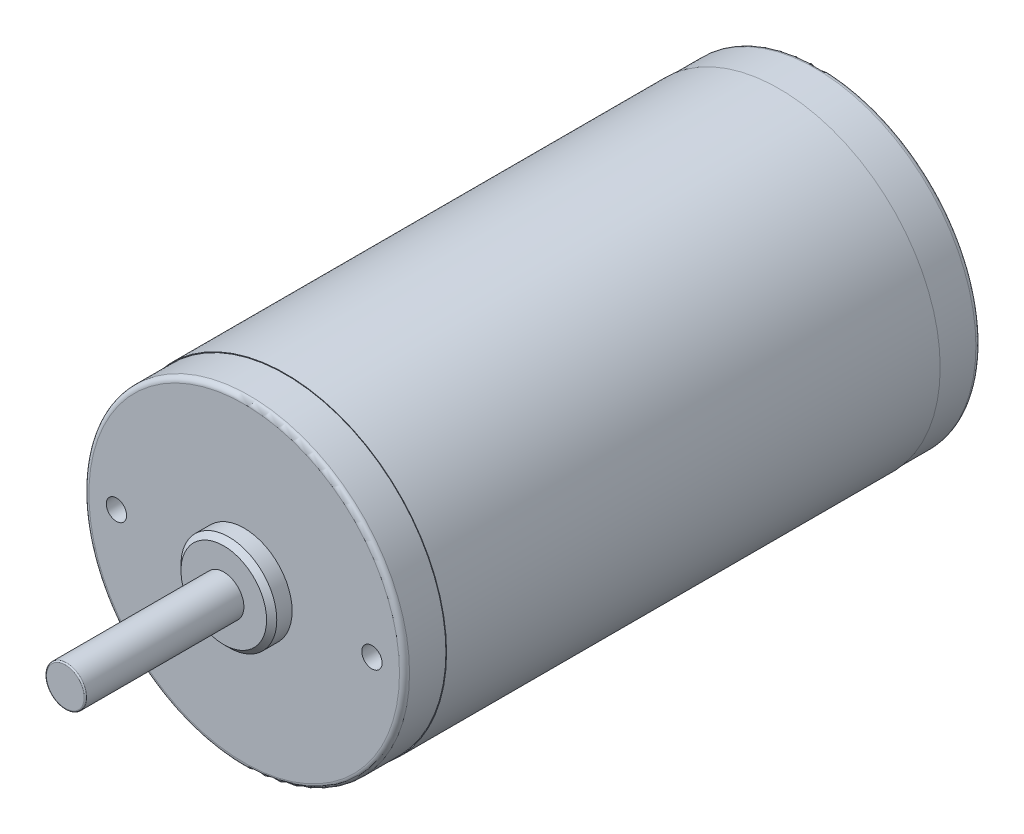
SolidWorks part; units mm, degrees
ref_plane "Front Plane" through (0, 0, 0) normal (0, 0, 1) x (1, 0, 0)
ref_plane "Top Plane" through (0, 0, 0) normal (0, 1, 0) x (1, 0, 0)
ref_plane "Right Plane" through (0, 0, 0) normal (1, 0, 0) x (0, 0, -1)
ref_plane "Plane1" through (0, 109.2962, 0) normal (0, -1, 0) x (1, 0, 0)
sketch "Sketch1" plane through (0, 109.2962, 0) normal (0, -1, 0) x (1, 0, 0)
  line L0 (67.564, 10.8204) -> (35.56, 10.8204)
  line L1 (35.56, 10.8204) -> (35.56, -87.3252)
  line L2 (35.56, -87.3252) -> (67.564, -87.3252)
  line L3 (67.564, -87.3252) -> (67.564, 10.8204)
  line L4 (35.56, 10.8204) -> (35.56, -87.3252) construction
revolve "Revolve1" add sketch "Sketch1" angle 360 about L4
sketch "Sketch2" plane through (0, 0, 10.8204) normal (0, 0, 1) x (1, 0, 0)
  circle A0 centre (35.56, 109.2962) radius 31.877
extrude "Boss-Extrude1" add sketch "Sketch2" along normal blind 8.2296
ref_plane "Plane2" through (0, 0, 18.542) normal (0, 0, -1) x (-1, 0, 0)
sketch "Sketch5" plane through (0, 0, 18.542) normal (0, 0, -1) x (-1, 0, 0)
  circle A0 centre (-35.56, 109.2962) radius 9.525
extrude "Boss-Extrude2" add sketch "Sketch5" against normal blind 4.572
sketch "Sketch6" plane through (0, 0, 23.114) normal (0, 0, 1) x (1, 0, 0)
  circle A0 centre (35.56, 109.2962) radius 4
extrude "Boss-Extrude3" add sketch "Sketch6" along normal blind 31.5
sketch "Sketch8" plane through (0, 0, -87.3252) normal (0, 0, -1) x (-1, 0, 0)
  circle A0 centre (-35.56, 109.2962) radius 31.877
extrude "Boss-Extrude4" add sketch "Sketch8" along normal blind 8.2296
sketch "Sketch9" plane through (0, 0, -95.5548) normal (0, 0, -1) x (-1, 0, 0)
  circle A0 centre (-35.56, 109.2962) radius 15.0368
extrude "Boss-Extrude5" add sketch "Sketch9" along normal blind 4.7625
ref_plane "Plane3" [suppressed] through (0, 120.5036, 0) normal (0, 1, 0) x (-1, 0, 0)
ref_plane "Plane4" [suppressed] through (0, 127.9033, 0) normal (0, 1, 0) x (-1, 0, 0)
hole_wizard "Hole2" positions "Sketch13" profile "Sketch12" legacy
sketch "Sketch13" plane through (0, 0, 19.05) normal (0, 0, 1) x (1, 0, 0)
  point P0 (60.96, 109.2962)
sketch "Sketch12" plane through (60.96, 109.2962, 19.05) normal (1, 0, 0) x (0, -1, 0)
  line L0 (0, 0) -> (0, 14.8277)
  line L1 (0, 14.8277) -> (2.0193, 13.6144)
  line L2 (2.0193, 13.6144) -> (2.0193, 0)
  line L4 (2.0193, 0) -> (0, 0)
  line L6 (0, 14.8277) -> (-2.0193, 13.6144) construction
  line L7 (0, -4.2442) -> (0, 117.3081) construction
  dimension "Diameter" = 4.0386
  dimension "Depth" = 13.6144
  dimension "Drill Angle" = 118
hole_wizard "Hole3" positions "Sketch15" profile "Sketch14" legacy
sketch "Sketch15" plane through (0, 0, 19.05) normal (0, 0, 1) x (1, 0, 0)
  point P0 (10.16, 109.2962)
sketch "Sketch14" plane through (10.16, 109.2962, 19.05) normal (1, 0, 0) x (0, -1, 0)
  line L0 (0, 0) -> (0, 14.8277)
  line L1 (0, 14.8277) -> (2.0193, 13.6144)
  line L2 (2.0193, 13.6144) -> (2.0193, 0)
  line L4 (2.0193, 0) -> (0, 0)
  line L6 (0, 14.8277) -> (-2.0193, 13.6144) construction
  line L7 (0, -4.2442) -> (0, 117.3081) construction
  dimension "Diameter" = 4.0386
  dimension "Depth" = 13.6144
  dimension "Drill Angle" = 118
chamfer "Chamfer1" distance 1.016 angle 45 1 edges at (45.085, 109.2962, 23.114)
fillet "Fillet1" radius 0.254 1 edges at (39.56, 109.2962, 54.614)
fillet "Fillet2" radius 1 1 edges at (3.683, 109.2962, -95.5548)
fillet "Fillet3" radius 1 1 edges at (67.437, 109.2962, 19.05)
fillet "Fillet4" radius 1 1 edges at (20.5232, 109.2962, -100.3173)
ref_plane "Plane5" [suppressed] through (39.56, 0, 0) normal (1, 0, 0) x (0, 0, -1)
